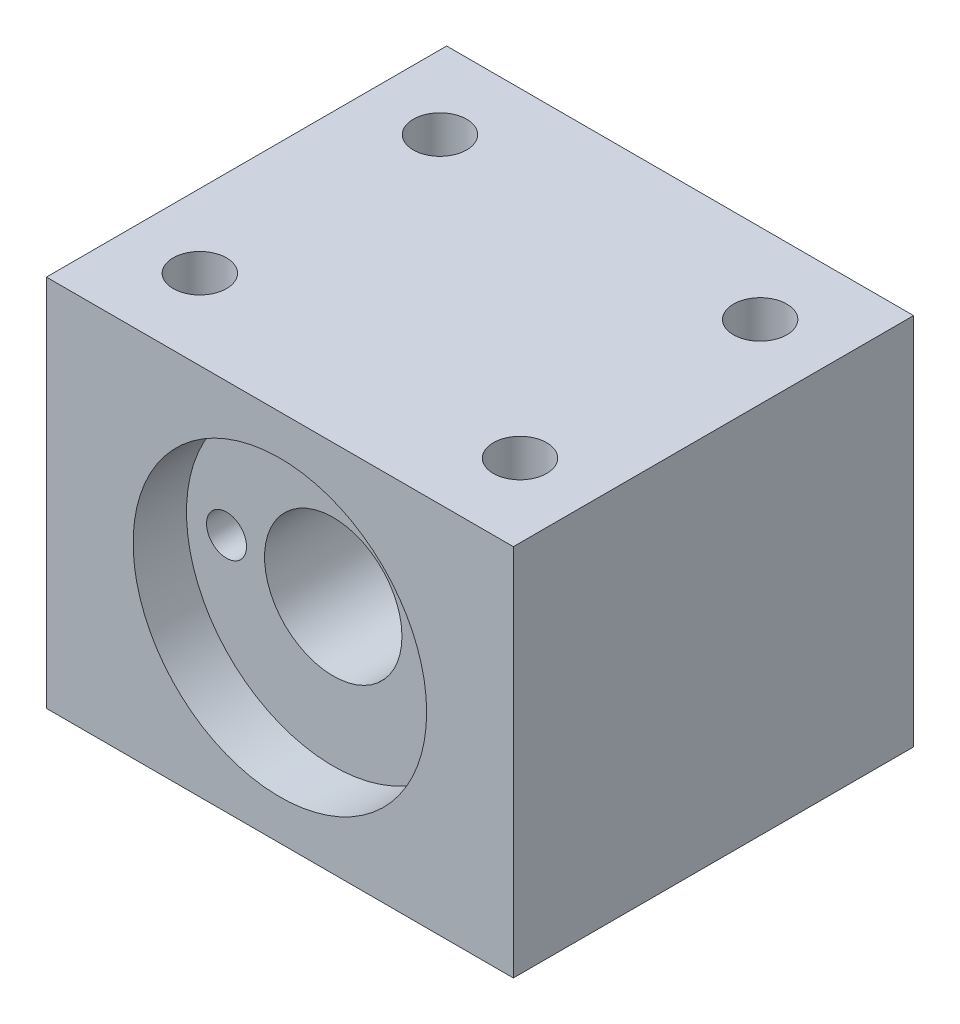
SolidWorks part; units mm, degrees
ref_plane "Plano frontal" through (0, 0, 0) normal (0, 0, 1) x (1, 0, 0)
ref_plane "Plano superior" through (0, 0, 0) normal (0, 1, 0) x (1, 0, 0)
ref_plane "Plano direito" through (0, 0, 0) normal (1, 0, 0) x (0, 0, -1)
sketch "Esboço1" plane through (0, 0, 0) normal (0, 0, 1) x (1, 0, 0)
  line L1 (17.5, -14) -> (-17.5, -14)
  line L2 (17.5, -14) -> (17.5, 14)
  line L3 (17.5, 14) -> (-17.5, 14)
  line L4 (-17.5, -14) -> (-17.5, 14)
  line L5 (17.5, -14) -> (-17.5, 14) construction
  line L6 (17.5, 14) -> (-17.5, -14) construction
  point P0 (0, 0)
  dimension "D1" = 28
  dimension "D2" = 35
extrude "Ressalto-extrusão1" add sketch "Esboço1" along normal blind 30
sketch "Esboço2" plane through (0, 0, 30) normal (0, 0, 1) x (1, 0, 0)
  circle A0 centre (0, 0) radius 5.15
  dimension "D1" = 10.3
extrude "Corte-extrusão1" cut sketch "Esboço2" against normal through all
sketch "Esboço3" plane through (0, 0, 30) normal (0, 0, 1) x (1, 0, 0)
  circle A0 centre (0, 0) radius 11
  dimension "D1" = 22
extrude "Corte-extrusão2" cut sketch "Esboço3" against normal blind 4
sketch "Esboço4" plane through (0, 0, 26) normal (0, 0, 1) x (1, 0, 0)
  line L0 (-21.4049, 0) -> (21.1109, 0) construction
  line L1 (0, -8.2033) -> (0, 8.2621) construction
  circle A0 centre (-8, 0) radius 1.5
  circle A2 centre (8, 0) radius 1.5
  dimension "D1" = 3
  dimension "D2" = 8
extrude "Corte-extrusão3" cut sketch "Esboço4" against normal blind 10
sketch "Esboço6" plane through (0, 14, 0) normal (0, 1, 0) x (1, 0, 0)
  line L0 (0, -32.2949) -> (0, 3.5537) construction
  line L1 (-23.7705, -15) -> (24.95, -15) construction
  line L2 (-17.5, -30) -> (-17.5, 0) construction
  circle A0 centre (-12, -24) radius 2
  circle A1 centre (12, -24) radius 2
  circle A2 centre (12, -6) radius 2
  circle A3 centre (-12, -6) radius 2
  dimension "D1" = 4
  dimension "D2" = 5.5
  dimension "D3" = 9
extrude "Corte-extrusão4" cut sketch "Esboço6" against normal blind 7
